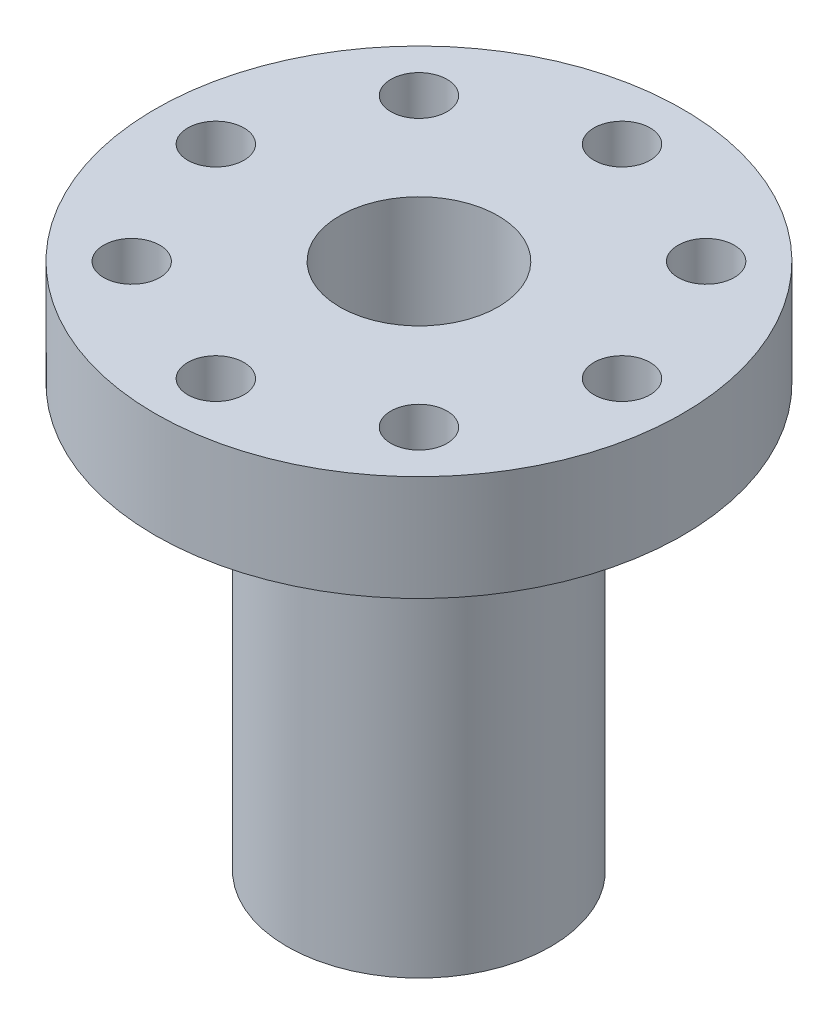
SolidWorks part; units mm, degrees
ref_plane "Front Plane" through (0, 0, 0) normal (0, 0, 1) x (1, 0, 0)
ref_plane "Top Plane" through (0, 0, 0) normal (0, 1, 0) x (1, 0, 0)
ref_plane "Right Plane" through (0, 0, 0) normal (1, 0, 0) x (0, 0, -1)
sketch "Sketch1" plane through (0, 0, 0) normal (0, 0, 1) x (1, 0, 0)
  line L0 (12.7, 0) -> (0, 0)
  line L1 (0, 0) -> (0, -25.4)
  line L2 (0, -25.4) -> (6.35, -25.4)
  line L3 (6.35, -25.4) -> (6.35, -5.08)
  line L4 (6.35, -5.08) -> (12.7, -5.08)
  line L5 (12.7, -5.08) -> (12.7, 0)
  dimension "D1" = 25.4
  dimension "D2" = 20.32
  dimension "D3" = 6.35
  dimension "D4" = 12.7
revolve "Revolve1" add sketch "Sketch1" angle 360 about L1
hole_wizard "#6-32 Tapped Hole1" positions "Sketch3" profile "Sketch4" tap size "#6-32" standard "ANSI Inch"
sketch "Sketch3" plane through (0, 0, 0) normal (0, 1, 0) x (1, 0, 0)
  point P0 (0, -9.779)
  dimension "D1" = 9.779
sketch "Sketch4" plane through (0, 0, 9.779) normal (1, 0, 0) x (0, 0, 1)
  line L0 (0, 0) -> (0, 10.2107)
  line L1 (0, 10.2107) -> (1.3525, 9.398)
  line L2 (1.3525, 9.398) -> (1.3525, 0)
  line L5 (1.3525, 0) -> (0, 0)
  line L10 (0, 10.2107) -> (-1.3526, 9.398) construction
  line L11 (0, -6.35) -> (0, 107.95) construction
  dimension "Tap Drill Dia." = 2.7051
  dimension "Tap Drill Depth" = 9.398
  dimension "Drill Angle" = 118
cosmetic thread "Hole Thread1" parameters "D1"=5.08, "D2"=3.5052
pattern_circular "CirPattern1" count 8 over 360 about axis through (0, 0, 0) along (0, 1, 0) of "#6-32 Tapped Hole1"
sketch "Sketch5" plane through (0, 0, 0) normal (0, 1, 0) x (1, 0, 0)
  circle A0 centre (0, 0) radius 3.81
  dimension "D1" = 7.62
extrude "Cut-Extrude1" cut sketch "Sketch5" against normal blind 20.828
sketch "Sketch6" plane through (0, -20.828, 0) normal (0, 1, 0) x (1, 0, 0)
  circle A0 centre (0, 0) radius 1.4986
  dimension "D1" = 2.9972
extrude "Cut-Extrude2" cut sketch "Sketch6" against normal through all
